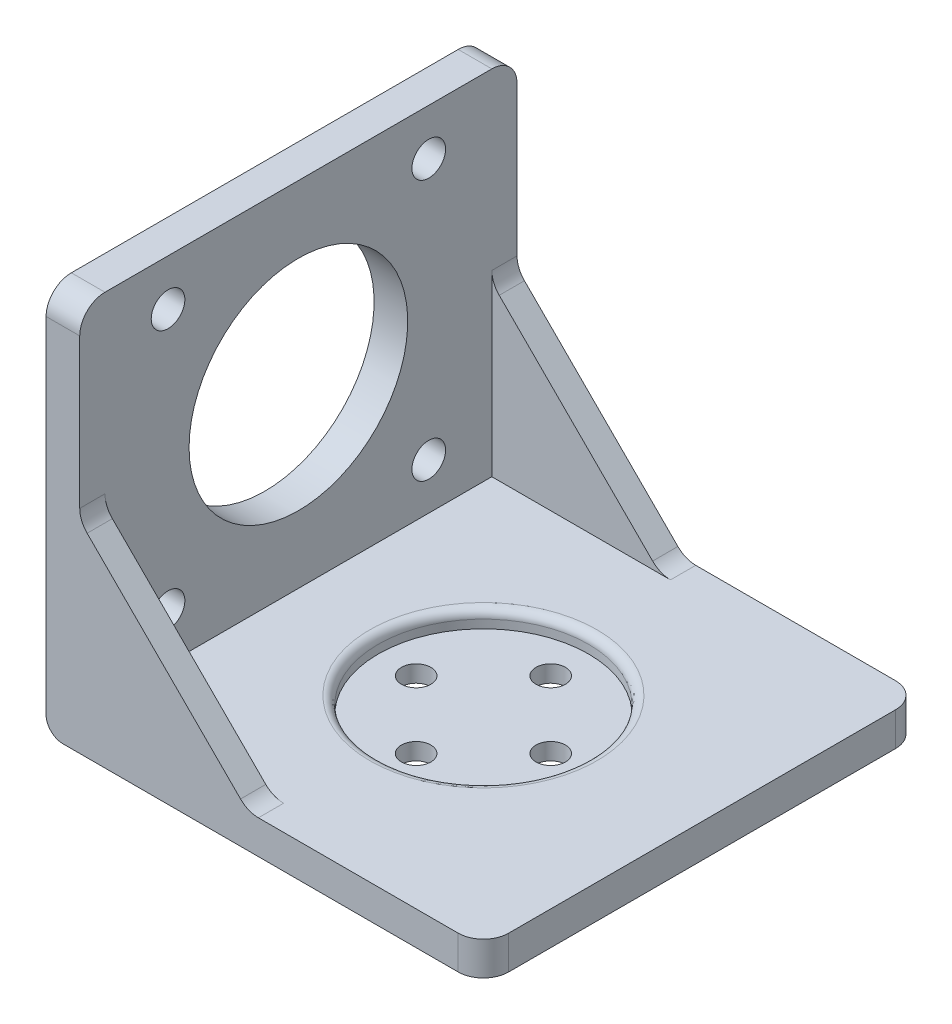
SolidWorks part; units mm, degrees
ref_plane "前视基准面" through (0, 0, 0) normal (0, 0, 1) x (1, 0, 0)
ref_plane "上视基准面" through (0, 0, 0) normal (0, 1, 0) x (1, 0, 0)
ref_plane "右视基准面" through (0, 0, 0) normal (1, 0, 0) x (0, 0, -1)
other "Configuration Table"
sketch "草图1" plane through (0, 0, 0) normal (0, 1, 0) x (1, 0, 0)
  line L1 (-26, -23) -> (26, -23)
  line L2 (-26, -23) -> (-26, 23)
  line L3 (-26, 23) -> (26, 23)
  line L4 (26, -23) -> (26, 23)
  line L5 (-26, -23) -> (26, 23) construction
  line L6 (-26, 23) -> (26, -23) construction
  circle A0 centre (8, 0) radius 1.75
  circle A1 centre (0, 8) radius 1.75
  circle A2 centre (-8, 0) radius 1.75
  circle A3 centre (0, -8) radius 1.75
  point P0 (0, 0)
  dimension "D3" = 3.5
  dimension "D10" = 3.5
  dimension "D11" = 3.5
  dimension "D13" = 3.5
  dimension "D1" = 46
  dimension "D2" = 52
  dimension "D4" = 16
  dimension "D5" = 16
  dimension "D6" = 0
  dimension "D7" = 0
  dimension "D8" = 15
  dimension "D9" = 26
  dimension "D12" = 18
  dimension "D14" = 23
extrude "凸台-拉伸2" add sketch "草图1" along normal blind 4
sketch "草图2" plane through (-26, 0, 0) normal (-1, 0, 0) x (0, 0, 1)
  line L0 (23, 4) -> (-23, 4)
  line L1 (23, 4) -> (23, 46)
  line L2 (-23, 4) -> (-23, 46)
  line L3 (23, 46) -> (-23, 46)
  circle A0 centre (15.5, 40.5) radius 2
  circle A1 centre (15.5, 9.5) radius 2
  circle A2 centre (-15.5, 9.5) radius 2
  circle A3 centre (-15.5, 40.5) radius 2
  circle A4 centre (0, 25) radius 13
  dimension "D2" = 4
  dimension "D3" = 4
  dimension "D4" = 4
  dimension "D5" = 4
  dimension "D14" = 26
  dimension "D1" = 42
  dimension "D6" = 31
  dimension "D7" = 31
  dimension "D8" = 31
  dimension "D9" = 7.5
  dimension "D10" = 5.5
  dimension "D11" = 0
  dimension "D12" = 0
  dimension "D13" = 0
  dimension "D15" = 21
  dimension "D16" = 23
extrude "凸台-拉伸3" add sketch "草图2" against normal blind 4
sketch "草图4" plane through (0, 4, 0) normal (0, 1, 0) x (1, 0, 0)
  circle A0 centre (0, 0) radius 12.5
  dimension "D1" = 25
extrude "切除-拉伸1" cut sketch "草图4" against normal blind 2
sketch "草图6" plane through (0, 0, 23) normal (0, 0, 1) x (1, 0, 0)
  line L0 (-26, 46) -> (-22, 46)
  line L1 (-22, 46) -> (-22, 24)
  line L2 (-22, 4) -> (-22, 46) construction
  line L3 (-22, 24) -> (-2, 4)
  line L4 (-22, 4) -> (26, 4) construction
  line L5 (-2, 4) -> (26, 4)
  line L6 (26, 4) -> (26, 0)
  line L7 (26, 0) -> (-26, 0)
  line L8 (-26, 0) -> (-26, 46)
  dimension "D1" = 20
  dimension "D2" = 20
extrude "凸台-拉伸4" add sketch "草图6" along normal blind 3 contours L8 L0 L1 L3 L5 L6 L7
sketch "草图7" plane through (0, 0, -23) normal (0, 0, -1) x (-1, 0, 0)
  line L0 (26, 46) -> (26, 0)
  line L1 (26, 0) -> (-26, 0)
  line L2 (-26, 0) -> (-26, 4)
  line L3 (-26, 4) -> (2, 4)
  line L4 (-26, 4) -> (22, 4) construction
  line L5 (22, 4) -> (2, 4) construction
  line L6 (2, 4) -> (22, 24)
  line L7 (22, 46) -> (22, 4) construction
  line L8 (22, 4) -> (22, 24) construction
  line L9 (22, 24) -> (22, 46)
  line L10 (22, 46) -> (26, 46) construction
  line L11 (22, 46) -> (26, 46)
  dimension "D1" = 20
  dimension "D2" = 20
extrude "凸台-拉伸5" add sketch "草图7" along normal blind 3
fillet "圆角1" radius 3 1 edges at (-24, 46, 26)
fillet "圆角2" radius 3 1 edges at (-24, 46, -26)
fillet "圆角3" radius 3 1 edges at (26, 2, 26)
fillet "圆角4" radius 3 1 edges at (26, 2, -26)
fillet "圆角5" radius 3 1 edges at (-22, 24, 24.5)
fillet "圆角6" radius 3 1 edges at (-2, 4, 24.5)
fillet "圆角7" radius 3 1 edges at (-22, 24, -24.5)
fillet "圆角8" radius 3 1 edges at (-2, 4, -24.5)
fillet "圆角9" radius 1 1 edges at (0, 4, 12.5)
fillet "圆角10" radius 2 1 edges at (-26, 0, 0)
